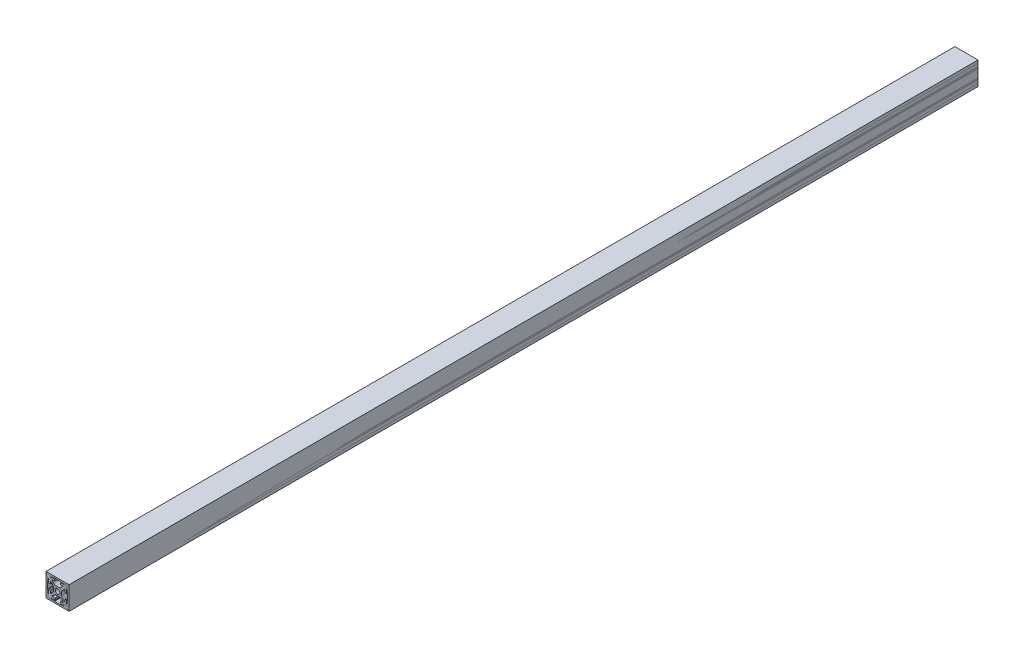
SolidWorks part; units mm, degrees
other "1x1\" Box"
other "1010 Imperial"
other "2020 Metric"
ref_plane "Front Plane" through (0, 0, 0) normal (0, 0, 1) x (1, 0, 0)
ref_plane "Top Plane" through (0, 0, 0) normal (0, 1, 0) x (1, 0, 0)
ref_plane "Right Plane" through (0, 0, 0) normal (1, 0, 0) x (0, 0, -1)
sketch "2020" plane through (0, 0, 0) normal (0, 0, 1) x (1, 0, 0)
  line L0 (8.25, 3) -> (9.75, 3)
  line L1 (10, 3.25) -> (10, 9)
  line L2 (9, 10) -> (3.25, 10)
  line L3 (3, 9.75) -> (3, 8.25)
  line L4 (3.25, 8) -> (5.75, 8)
  line L5 (6, 7.75) -> (6, 7.1642)
  line L6 (5.9268, 6.9874) -> (3.0858, 4.1464)
  line L7 (2.7322, 4) -> (-2.7322, 4)
  line L8 (-3.0858, 4.1464) -> (-5.9268, 6.9874)
  line L9 (-6, 7.1642) -> (-6, 7.75)
  line L10 (-5.75, 8) -> (-3.25, 8)
  line L11 (-3, 8.25) -> (-3, 9.75)
  line L12 (-3.25, 10) -> (-9, 10)
  line L13 (-10, 9) -> (-10, 3.25)
  line L14 (-9.75, 3) -> (-8.25, 3)
  line L15 (-8, 3.25) -> (-8, 5.75)
  line L16 (-7.75, 6) -> (-7.1642, 6)
  line L17 (-6.9874, 5.9268) -> (-4.1464, 3.0858)
  line L18 (-4, 2.7322) -> (-4, -2.7322)
  line L19 (-4.1464, -3.0858) -> (-6.9874, -5.9268)
  line L20 (-7.1642, -6) -> (-7.75, -6)
  line L21 (-8, -5.75) -> (-8, -3.25)
  line L22 (-8.25, -3) -> (-9.75, -3)
  line L23 (-10, -3.25) -> (-10, -9)
  line L24 (-9, -10) -> (-3.25, -10)
  line L25 (-3, -9.75) -> (-3, -8.25)
  line L26 (-3.25, -8) -> (-5.75, -8)
  line L27 (-6, -7.75) -> (-6, -7.1642)
  line L28 (-5.9268, -6.9874) -> (-3.0858, -4.1464)
  line L29 (-2.7322, -4) -> (2.7322, -4)
  line L30 (3.0858, -4.1464) -> (5.9268, -6.9874)
  line L31 (6, -7.1642) -> (6, -7.75)
  line L32 (5.75, -8) -> (3.25, -8)
  line L33 (3, -8.25) -> (3, -9.75)
  line L34 (3.25, -10) -> (9, -10)
  line L35 (10, -9) -> (10, -3.25)
  line L36 (9.75, -3) -> (8.25, -3)
  line L37 (8, -3.25) -> (8, -5.75)
  line L38 (7.75, -6) -> (7.1642, -6)
  line L39 (6.9874, -5.9268) -> (4.1464, -3.0858)
  line L40 (4, -2.7322) -> (4, 2.7322)
  line L41 (4.1464, 3.0858) -> (6.9874, 5.9268)
  line L42 (7.1642, 6) -> (7.75, 6)
  line L43 (8, 5.75) -> (8, 3.25)
  circle A0 centre (0, 0) radius 2.5
  arc A1 (9.75, 3) -> (10, 3.25) centre (9.75, 3.25) ccw
  arc A2 (10, 9) -> (9, 10) centre (9, 9) ccw
  arc A3 (3.25, 10) -> (3, 9.75) centre (3.25, 9.75) ccw
  arc A4 (3, 8.25) -> (3.25, 8) centre (3.25, 8.25) ccw
  arc A5 (6, 7.75) -> (5.75, 8) centre (5.75, 7.75) ccw
  arc A6 (5.9268, 6.9874) -> (6, 7.1642) centre (5.75, 7.1642) ccw
  arc A7 (2.7322, 4) -> (3.0858, 4.1464) centre (2.7322, 4.5) ccw
  arc A8 (-3.0858, 4.1464) -> (-2.7322, 4) centre (-2.7322, 4.5) ccw
  arc A9 (-6, 7.1642) -> (-5.9268, 6.9874) centre (-5.75, 7.1642) ccw
  arc A10 (-5.75, 8) -> (-6, 7.75) centre (-5.75, 7.75) ccw
  arc A11 (-3.25, 8) -> (-3, 8.25) centre (-3.25, 8.25) ccw
  arc A12 (-3, 9.75) -> (-3.25, 10) centre (-3.25, 9.75) ccw
  arc A13 (-9, 10) -> (-10, 9) centre (-9, 9) ccw
  arc A14 (-10, 3.25) -> (-9.75, 3) centre (-9.75, 3.25) ccw
  arc A15 (-8.25, 3) -> (-8, 3.25) centre (-8.25, 3.25) ccw
  arc A16 (-7.75, 6) -> (-8, 5.75) centre (-7.75, 5.75) ccw
  arc A17 (-6.9874, 5.9268) -> (-7.1642, 6) centre (-7.1642, 5.75) ccw
  arc A18 (-4, 2.7322) -> (-4.1464, 3.0858) centre (-4.5, 2.7322) ccw
  arc A19 (-4.1464, -3.0858) -> (-4, -2.7322) centre (-4.5, -2.7322) ccw
  arc A20 (-7.1642, -6) -> (-6.9874, -5.9268) centre (-7.1642, -5.75) ccw
  arc A21 (-8, -5.75) -> (-7.75, -6) centre (-7.75, -5.75) ccw
  arc A22 (-8, -3.25) -> (-8.25, -3) centre (-8.25, -3.25) ccw
  arc A23 (-9.75, -3) -> (-10, -3.25) centre (-9.75, -3.25) ccw
  arc A24 (-10, -9) -> (-9, -10) centre (-9, -9) ccw
  arc A25 (-3.25, -10) -> (-3, -9.75) centre (-3.25, -9.75) ccw
  arc A26 (-3, -8.25) -> (-3.25, -8) centre (-3.25, -8.25) ccw
  arc A27 (-6, -7.75) -> (-5.75, -8) centre (-5.75, -7.75) ccw
  arc A28 (-5.9268, -6.9874) -> (-6, -7.1642) centre (-5.75, -7.1642) ccw
  arc A29 (-2.7322, -4) -> (-3.0858, -4.1464) centre (-2.7322, -4.5) ccw
  arc A30 (3.0858, -4.1464) -> (2.7322, -4) centre (2.7322, -4.5) ccw
  arc A31 (6, -7.1642) -> (5.9268, -6.9874) centre (5.75, -7.1642) ccw
  arc A32 (5.75, -8) -> (6, -7.75) centre (5.75, -7.75) ccw
  arc A33 (3.25, -8) -> (3, -8.25) centre (3.25, -8.25) ccw
  arc A34 (3, -9.75) -> (3.25, -10) centre (3.25, -9.75) ccw
  arc A35 (9, -10) -> (10, -9) centre (9, -9) ccw
  arc A36 (10, -3.25) -> (9.75, -3) centre (9.75, -3.25) ccw
  arc A37 (8.25, -3) -> (8, -3.25) centre (8.25, -3.25) ccw
  arc A38 (7.75, -6) -> (8, -5.75) centre (7.75, -5.75) ccw
  arc A39 (6.9874, -5.9268) -> (7.1642, -6) centre (7.1642, -5.75) ccw
  arc A40 (4, -2.7322) -> (4.1464, -3.0858) centre (4.5, -2.7322) ccw
  arc A41 (4.1464, 3.0858) -> (4, 2.7322) centre (4.5, 2.7322) ccw
  arc A42 (7.1642, 6) -> (6.9874, 5.9268) centre (7.1642, 5.75) ccw
  arc A43 (8, 5.75) -> (7.75, 6) centre (7.75, 5.75) ccw
  arc A44 (8, 3.25) -> (8.25, 3) centre (8.25, 3.25) ccw
extrude "Boss-Extrude1" add sketch "2020" along normal blind 1000 contours A0
sketch "Sketch2" plane through (0, 0, 0) normal (0, 0, 1) x (1, 0, 0)
  line L0 (-1.7093, -4.4958) -> (1.7093, -4.4958)
  line L1 (3.9523, -5.4237) -> (7.1797, -8.6452)
  line L2 (6.4164, -10.4902) -> (4.2875, -10.4902)
  line L3 (3.2385, -11.5392) -> (3.2385, -11.651)
  line L4 (4.2875, -12.7) -> (5.3171, -12.7)
  line L5 (6.3331, -12.7) -> (9.5504, -12.7)
  line L6 (12.7, -9.5504) -> (12.7, -6.3331)
  line L7 (12.7, -5.3171) -> (12.7, -4.2875)
  line L8 (11.651, -3.2385) -> (11.5392, -3.2385)
  line L9 (10.4902, -4.2875) -> (10.4902, -6.4021)
  line L10 (8.737, -7.1292) -> (5.4405, -3.8388)
  line L11 (4.5085, -1.5917) -> (4.5085, 1.5917)
  line L12 (5.4405, 3.8388) -> (8.737, 7.1292)
  line L13 (10.4902, 6.4021) -> (10.4902, 4.2875)
  line L14 (11.5392, 3.2385) -> (11.651, 3.2385)
  line L15 (12.7, 4.2875) -> (12.7, 5.3171)
  line L16 (12.7, 6.3331) -> (12.7, 9.5504)
  line L17 (9.5504, 12.7) -> (6.3331, 12.7)
  line L18 (5.3171, 12.7) -> (4.2875, 12.7)
  line L19 (3.2384, 11.651) -> (3.2384, 11.5392)
  line L20 (4.2875, 10.4902) -> (6.4768, 10.4902)
  line L21 (7.2072, 8.7245) -> (3.9003, 5.4237)
  line L22 (1.6573, 4.4958) -> (-1.6573, 4.4958)
  line L23 (-3.9003, 5.4237) -> (-7.2072, 8.7245)
  line L24 (-6.4768, 10.4902) -> (-4.2875, 10.4902)
  line L25 (-3.2384, 11.5392) -> (-3.2384, 11.651)
  line L26 (-4.2875, 12.7) -> (-5.3171, 12.7)
  line L27 (-6.3331, 12.7) -> (-9.5504, 12.7)
  line L28 (-12.7, 9.5504) -> (-12.7, 6.3331)
  line L29 (-12.7, 5.3171) -> (-12.7, 4.2875)
  line L30 (-11.651, 3.2385) -> (-11.5392, 3.2385)
  line L31 (-10.4902, 4.2875) -> (-10.4902, 6.4021)
  line L32 (-8.737, 7.1292) -> (-5.4405, 3.8388)
  line L33 (-4.5085, 1.5917) -> (-4.5085, -1.5917)
  line L34 (-5.4405, -3.8388) -> (-8.737, -7.1292)
  line L35 (-10.4902, -6.4021) -> (-10.4902, -4.2875)
  line L36 (-11.5392, -3.2385) -> (-11.651, -3.2385)
  line L37 (-12.7, -4.2875) -> (-12.7, -5.3171)
  line L38 (-12.7, -6.3331) -> (-12.7, -9.5504)
  line L39 (-9.5504, -12.7) -> (-6.3331, -12.7)
  line L40 (-5.3171, -12.7) -> (-4.2875, -12.7)
  line L41 (-3.2385, -11.651) -> (-3.2385, -11.5392)
  line L42 (-4.2875, -10.4902) -> (-6.4164, -10.4902)
  line L43 (-7.1797, -8.6452) -> (-3.9523, -5.4237)
  circle A0 centre (0, 0) radius 2.6035
  arc A1 (-1.7093, -4.4958) -> (-3.9523, -5.4237) centre (-1.7093, -7.6708) ccw
  arc A2 (3.9523, -5.4237) -> (1.7093, -4.4958) centre (1.7093, -7.6708) ccw
  arc A3 (6.4164, -10.4902) -> (7.1797, -8.6452) centre (6.4164, -9.4098) ccw
  arc A4 (4.2875, -10.4902) -> (3.2385, -11.5392) centre (4.2875, -11.5392) ccw
  arc A5 (3.2385, -11.651) -> (4.2875, -12.7) centre (4.2875, -11.651) ccw
  arc A6 (6.3331, -12.7) -> (5.3171, -12.7) centre (5.8251, -12.7) ccw
  arc A7 (10.5664, -12.6998) -> (9.5504, -12.7) centre (10.0584, -12.7) ccw
  arc A8 (10.5664, -12.6998) -> (12.6998, -10.5664) centre (10.5918, -10.5918) ccw
  arc A9 (12.7, -9.5504) -> (12.6998, -10.5664) centre (12.7, -10.0584) ccw
  arc A10 (12.7, -5.3171) -> (12.7, -6.3331) centre (12.7, -5.8251) ccw
  arc A11 (12.7, -4.2875) -> (11.651, -3.2385) centre (11.651, -4.2875) ccw
  arc A12 (11.5392, -3.2385) -> (10.4902, -4.2875) centre (11.5392, -4.2875) ccw
  arc A13 (8.737, -7.1292) -> (10.4902, -6.4021) centre (9.4628, -6.4021) ccw
  arc A14 (4.5085, -1.5917) -> (5.4405, -3.8388) centre (7.6835, -1.5917) ccw
  arc A15 (5.4405, 3.8388) -> (4.5085, 1.5917) centre (7.6835, 1.5917) ccw
  arc A16 (10.4902, 6.4021) -> (8.737, 7.1292) centre (9.4628, 6.4021) ccw
  arc A17 (10.4902, 4.2875) -> (11.5392, 3.2385) centre (11.5392, 4.2875) ccw
  arc A18 (11.651, 3.2385) -> (12.7, 4.2875) centre (11.651, 4.2875) ccw
  arc A19 (12.7, 6.3331) -> (12.7, 5.3171) centre (12.7, 5.8251) ccw
  arc A20 (12.6998, 10.5664) -> (12.7, 9.5504) centre (12.7, 10.0584) ccw
  arc A21 (12.6998, 10.5664) -> (10.5664, 12.6998) centre (10.5918, 10.5918) ccw
  arc A22 (9.5504, 12.7) -> (10.5664, 12.6998) centre (10.0584, 12.7) ccw
  arc A23 (5.3171, 12.7) -> (6.3331, 12.7) centre (5.8251, 12.7) ccw
  arc A24 (4.2875, 12.7) -> (3.2384, 11.651) centre (4.2875, 11.651) ccw
  arc A25 (3.2384, 11.5392) -> (4.2875, 10.4902) centre (4.2875, 11.5392) ccw
  arc A26 (7.2072, 8.7245) -> (6.4768, 10.4902) centre (6.4768, 9.4563) ccw
  arc A27 (1.6573, 4.4958) -> (3.9003, 5.4237) centre (1.6573, 7.6708) ccw
  arc A28 (-3.9003, 5.4237) -> (-1.6573, 4.4958) centre (-1.6573, 7.6708) ccw
  arc A29 (-6.4768, 10.4902) -> (-7.2072, 8.7245) centre (-6.4768, 9.4563) ccw
  arc A30 (-4.2875, 10.4902) -> (-3.2384, 11.5392) centre (-4.2875, 11.5392) ccw
  arc A31 (-3.2384, 11.651) -> (-4.2875, 12.7) centre (-4.2875, 11.651) ccw
  arc A32 (-6.3331, 12.7) -> (-5.3171, 12.7) centre (-5.8251, 12.7) ccw
  arc A33 (-10.5664, 12.6998) -> (-9.5504, 12.7) centre (-10.0584, 12.7) ccw
  arc A34 (-10.5664, 12.6998) -> (-12.6998, 10.5664) centre (-10.5918, 10.5918) ccw
  arc A35 (-12.7, 9.5504) -> (-12.6998, 10.5664) centre (-12.7, 10.0584) ccw
  arc A36 (-12.7, 5.3171) -> (-12.7, 6.3331) centre (-12.7, 5.8251) ccw
  arc A37 (-12.7, 4.2875) -> (-11.651, 3.2385) centre (-11.651, 4.2875) ccw
  arc A38 (-11.5392, 3.2385) -> (-10.4902, 4.2875) centre (-11.5392, 4.2875) ccw
  arc A39 (-8.737, 7.1292) -> (-10.4902, 6.4021) centre (-9.4628, 6.4021) ccw
  arc A40 (-4.5085, 1.5917) -> (-5.4405, 3.8388) centre (-7.6835, 1.5917) ccw
  arc A41 (-5.4405, -3.8388) -> (-4.5085, -1.5917) centre (-7.6835, -1.5917) ccw
  arc A42 (-10.4902, -6.4021) -> (-8.737, -7.1292) centre (-9.4628, -6.4021) ccw
  arc A43 (-10.4902, -4.2875) -> (-11.5392, -3.2385) centre (-11.5392, -4.2875) ccw
  arc A44 (-11.651, -3.2385) -> (-12.7, -4.2875) centre (-11.651, -4.2875) ccw
  arc A45 (-12.7, -6.3331) -> (-12.7, -5.3171) centre (-12.7, -5.8251) ccw
  arc A46 (-12.6998, -10.5664) -> (-12.7, -9.5504) centre (-12.7, -10.0584) ccw
  arc A47 (-12.6998, -10.5664) -> (-10.5664, -12.6998) centre (-10.5918, -10.5918) ccw
  arc A48 (-9.5504, -12.7) -> (-10.5664, -12.6998) centre (-10.0584, -12.7) ccw
  arc A49 (-5.3171, -12.7) -> (-6.3331, -12.7) centre (-5.8251, -12.7) ccw
  arc A50 (-4.2875, -12.7) -> (-3.2385, -11.651) centre (-4.2875, -11.651) ccw
  arc A51 (-3.2385, -11.5392) -> (-4.2875, -10.4902) centre (-4.2875, -11.5392) ccw
  arc A52 (-7.1797, -8.6452) -> (-6.4164, -10.4902) centre (-6.4164, -9.4098) ccw
extrude "Boss-Extrude2" add sketch "Sketch2" along normal blind 1000 separate body
sketch "Sketch3" plane through (0, 0, 0) normal (0, 0, 1) x (1, 0, 0)
  line L0 (-11.1125, -11.1125) -> (-11.1125, 11.1125)
  line L1 (12.7, -12.7) -> (-12.7, -12.7)
  line L2 (12.7, -12.7) -> (12.7, 12.7)
  line L3 (12.7, 12.7) -> (-12.7, 12.7)
  line L4 (-12.7, -12.7) -> (-12.7, 12.7)
  line L5 (12.7, -12.7) -> (-12.7, 12.7) construction
  line L6 (12.7, 12.7) -> (-12.7, -12.7) construction
  line L7 (11.1125, 11.1125) -> (-11.1125, 11.1125)
  line L8 (11.1125, -11.1125) -> (11.1125, 11.1125)
  line L9 (11.1125, -11.1125) -> (-11.1125, -11.1125)
  point P0 (0, 0)
  dimension "D1" = 25.4
  dimension "D2" = 25.4
  dimension "D3" = 1.5875
extrude "Boss-Extrude3" add sketch "Sketch3" along normal blind 1000 separate body
